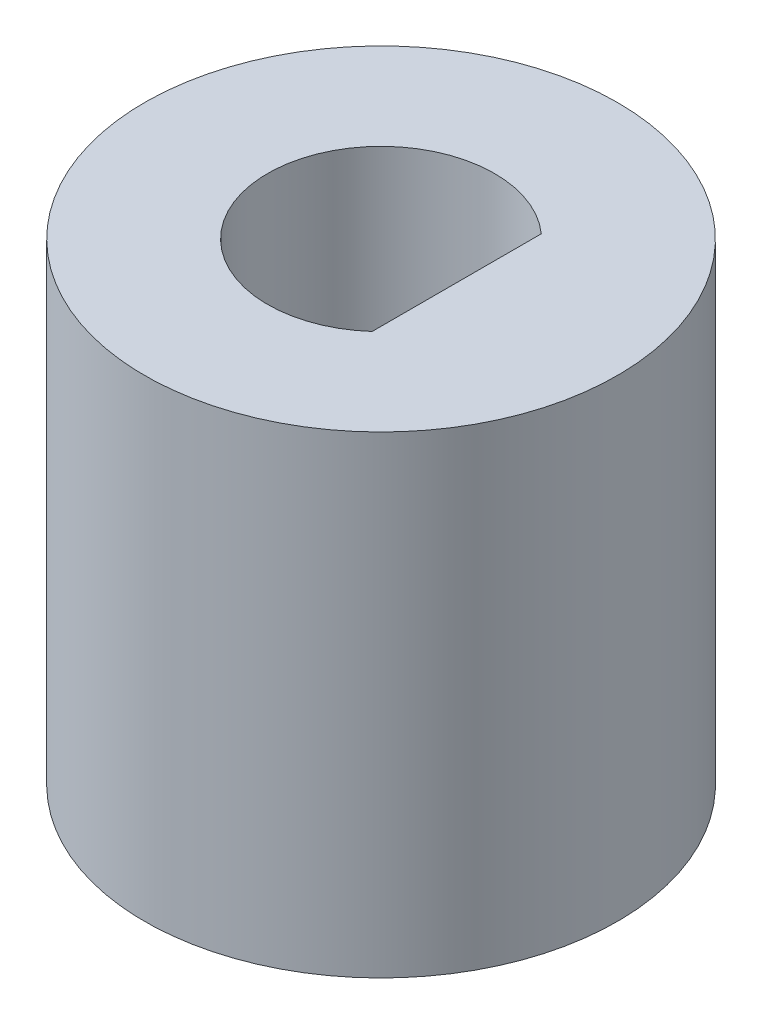
SolidWorks part; units mm, degrees
ref_plane "Plano frontal" through (0, 0, 0) normal (0, 0, 1) x (1, 0, 0)
ref_plane "Plano superior" through (0, 0, 0) normal (0, 1, 0) x (1, 0, 0)
ref_plane "Plano direito" through (0, 0, 0) normal (1, 0, 0) x (0, 0, -1)
sketch "Esboço1" plane through (0, 0, 0) normal (0, 0, 1) x (1, 0, 0)
  line L0 (-1, 10) -> (-5, 10)
  line L1 (-5, 10) -> (-5, 0)
  line L2 (-5, 0) -> (-2, 0)
  line L3 (0, 0) -> (0, 7.2368) construction
  line L4 (-2, 5) -> (-1, 5)
  line L5 (-2, 0) -> (-2, 5)
  line L6 (-1, 5) -> (-1, 10)
  dimension "D1" = 4
  dimension "D2" = 10
  dimension "D3" = 10
  dimension "D4" = 2
revolve "Revolução1" add sketch "Esboço1" angle 360 about L3
sketch "Esboço2" plane through (0, 10, 0) normal (0, 1, 0) x (1, 0, 0)
  line L0 (0, 0) -> (2, 0) construction
  line L1 (1.6, 1.7889) -> (1.6, -1.7889)
  arc A0 (1.6, 1.7889) -> (1.6, -1.7889) centre (0, 0) ccw
  dimension "D1" = 4.8
  dimension "D2" = 1.6
extrude "Corte-extrusão1" cut sketch "Esboço2" against normal blind 5
sketch "Esboço3" plane through (0, 0, 0) normal (0, -1, 0) x (1, 0, 0)
  line L0 (0.5, -2.7732) -> (0.5, 2.7051)
  line L1 (0.5, 2.7051) -> (3.0132, 2.7051)
  line L2 (3.0132, 2.7051) -> (3.0132, -2.7732)
  line L3 (3.0132, -2.7732) -> (0.5, -2.7732)
  dimension "D1" = 0.5
extrude "Ressalto-extrusão1" add sketch "Esboço3" against normal blind 5
